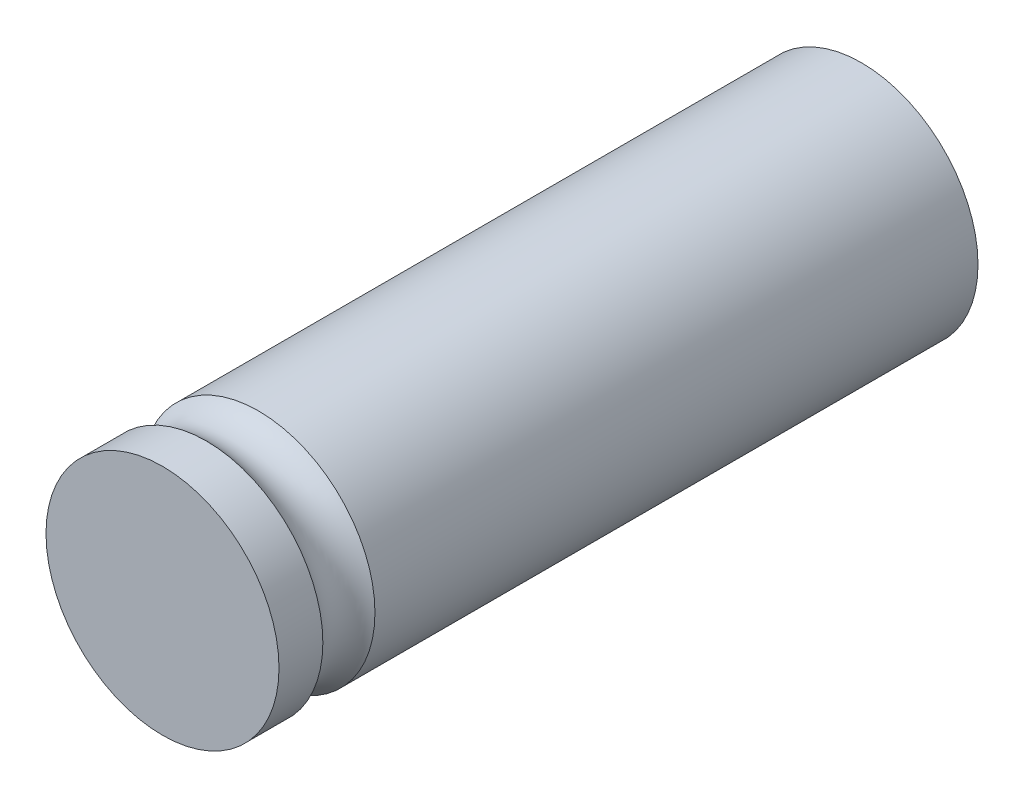
SolidWorks part; units mm, degrees
ref_plane "Plan de face" through (0, 0, 0) normal (0, 0, 1) x (1, 0, 0)
ref_plane "Plan de dessus" through (0, 0, 0) normal (0, 1, 0) x (1, 0, 0)
ref_plane "Plan de droite" through (0, 0, 0) normal (1, 0, 0) x (0, 0, -1)
ref_axis "Axe2" through (0, 0, -1.5) along (0, 0, 1)
sketch "Esquisse1" plane through (0, 0, 0) normal (0, 0, 1) x (1, 0, 0)
  circle A0 centre (0, 0) radius 5
  dimension "D1" = 10
extrude "Boss.-Extru.1" add sketch "Esquisse1" along normal blind 30
sketch "Esquisse2" plane through (0, 0, 0) normal (1, 0, 0) x (0, 0, -1)
  line L1 (-30, 5) -> (-30, -5) construction
  line L2 (1.5, 0) -> (-31.5, 0) construction
  circle A0 centre (-27, 6) radius 1.5
  dimension "D1" = 3
  dimension "D2" = 3
  dimension "D3" = 6
revolve "Enlèvement de matière-Révolution1" cut sketch "Esquisse2" angle 360 about axis through (0, 0, -1.5) along (0, 0, 1)
